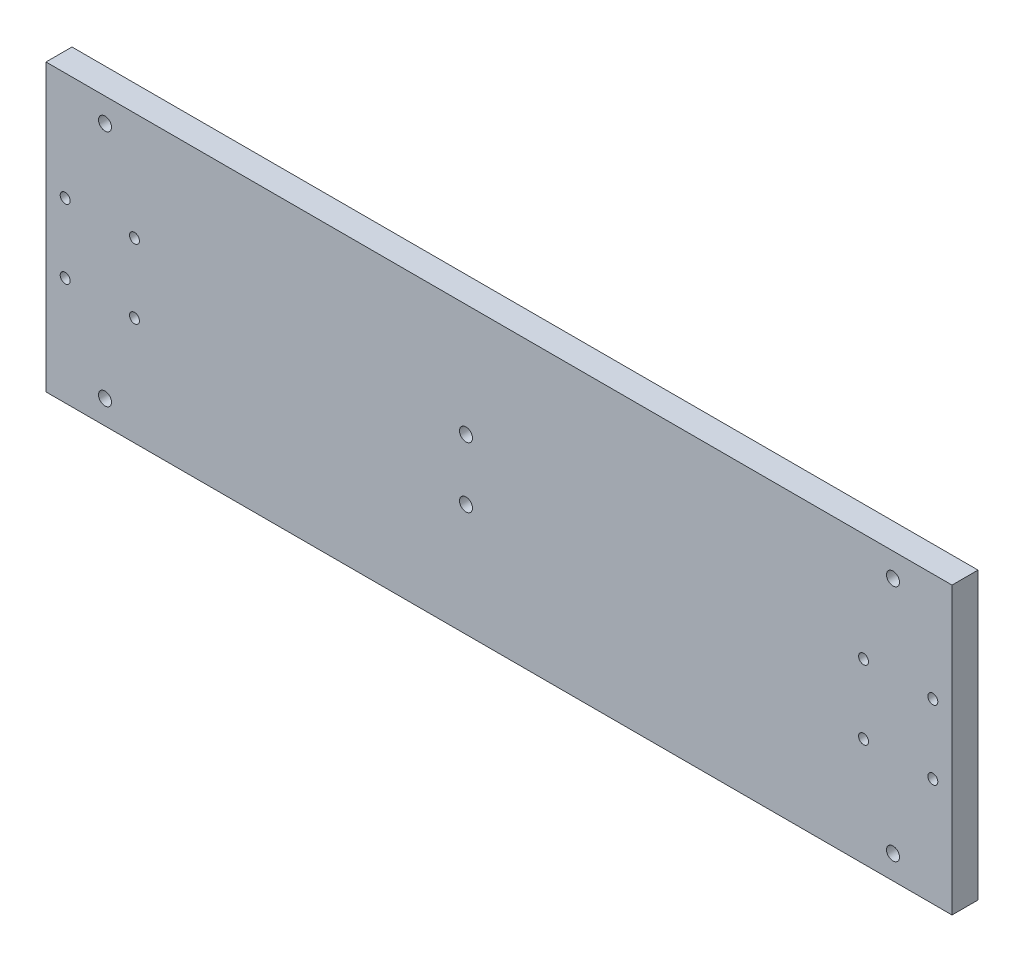
SolidWorks part; units mm, degrees
ref_plane "Plan de face" through (0, 0, 0) normal (0, 0, 1) x (1, 0, 0)
ref_plane "Plan de dessus" through (0, 0, 0) normal (0, 1, 0) x (1, 0, 0)
ref_plane "Plan de droite" through (0, 0, 0) normal (1, 0, 0) x (0, 0, -1)
sketch "Esquisse1" plane through (0, 0, 0) normal (0, 0, 1) x (1, 0, 0)
  line L1 (-104.63, 33) -> (104.63, 33)
  line L2 (-104.63, 33) -> (-104.63, -33)
  line L3 (-104.63, -33) -> (104.63, -33)
  line L4 (104.63, 33) -> (104.63, -33)
  dimension "D1" = 209.26
  dimension "D2" = 66
  dimension "D3" = 104.63
  dimension "D4" = 33
extrude "Boss.-Extru.1" add sketch "Esquisse1" along normal blind 6
sketch "Esquisse2" plane through (0, 0, 6) normal (0, 0, 1) x (1, 0, 0)
  line L0 (0, 49.0616) -> (0, -42.9956) construction
  line L1 (-104.63, 33) -> (-104.63, -33) construction
  line L2 (-104.63, -33) -> (104.63, -33) construction
  line L3 (91, 32.7086) -> (91, -49.0227) construction
  line L5 (-104.63, 33) -> (-104.63, -33) construction
  line L6 (-91, 32.7086) -> (-91, -49.0227) construction
  line L7 (104.63, -33) -> (104.63, 33) construction
  circle A0 centre (-100.2, 8) radius 1.15
  circle A1 centre (-84.2, 8) radius 1.15
  circle A2 centre (-84.2, -8) radius 1.15
  circle A3 centre (-100.2, -8) radius 1.15
  circle A4 centre (100.2, -8) radius 1.15
  circle A5 centre (84.2, -8) radius 1.15
  circle A6 centre (84.2, 8) radius 1.15
  circle A7 centre (100.2, 8) radius 1.15
  circle A8 centre (-7.625, 7) radius 1.5
  circle A9 centre (-7.625, -7) radius 1.5
  circle A10 centre (91, 27.5) radius 1.5
  circle A11 centre (91, -27.5) radius 1.5
  circle A12 centre (-91, -27.5) radius 1.5
  circle A13 centre (-91, 27.5) radius 1.5
  dimension "D1" = 2.3
  dimension "D2" = 2.3
  dimension "D3" = 2.3
  dimension "D4" = 2.3
  dimension "D12" = 3
  dimension "D14" = 3
  dimension "D13" = 26
  dimension "D15" = 7.625
  dimension "D19" = 3
  dimension "D20" = 3
  dimension "D21" = 55
  dimension "D22" = 5.5
  dimension "D5" = 4.43
  dimension "D6" = 25
  dimension "D7" = 25
  dimension "D8" = 16
  dimension "D9" = 16
  dimension "D10" = 16
  dimension "D11" = 16
  dimension "D16" = 14
  dimension "D17" = 7.625
  dimension "D18" = 4.43
  dimension "D23" = 13.63
extrude "Enlèv. mat.-Extru.1" cut sketch "Esquisse2" against normal blind 6
equation "\"D3@Esquisse1\"=\"D1@Esquisse1\"/2"
equation "\"D4@Esquisse1\"=\"D2@Esquisse1\"/2"
